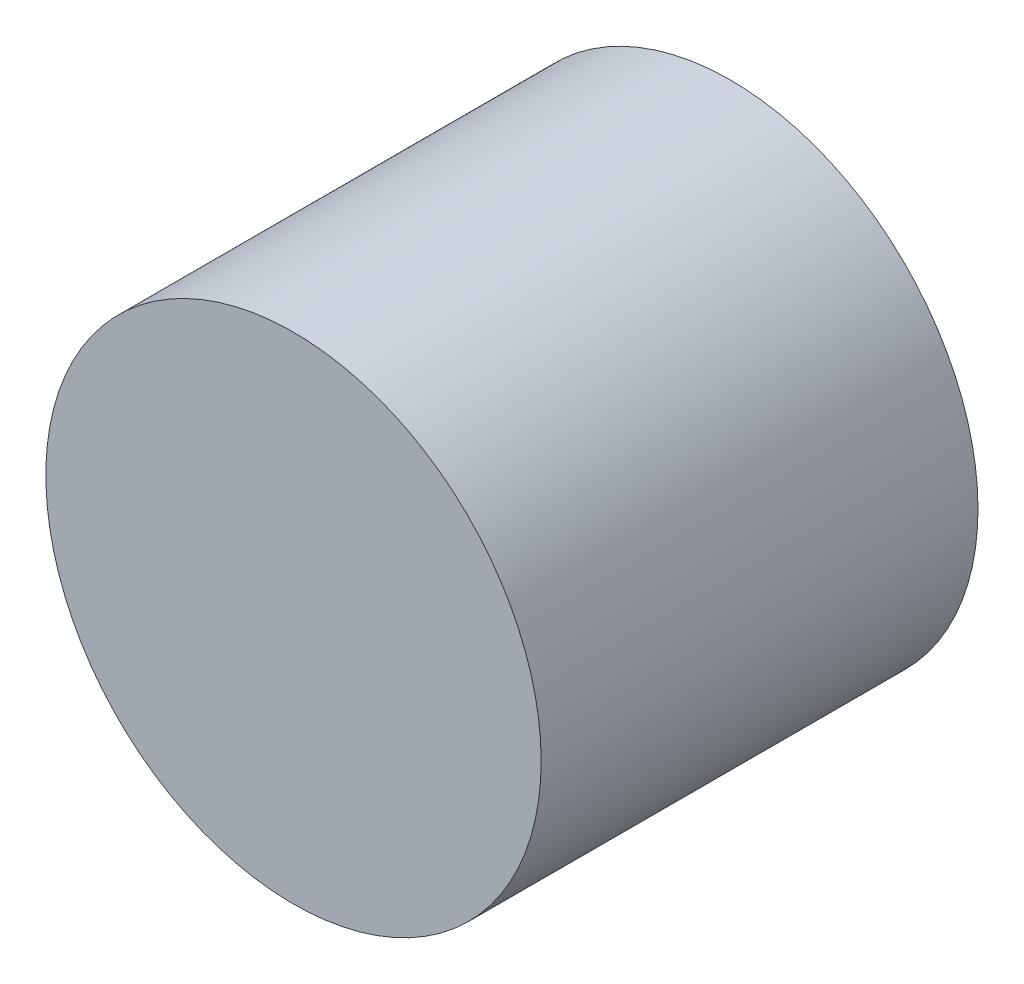
SolidWorks part; units mm, degrees
ref_plane "Front Plane" through (0, 0, 0) normal (0, 0, 1) x (1, 0, 0)
ref_plane "Top Plane" through (0, 0, 0) normal (0, 1, 0) x (1, 0, 0)
ref_plane "Right Plane" through (0, 0, 0) normal (1, 0, 0) x (0, 0, -1)
sketch "Sketch1" plane through (0, 0, 0) normal (0, 0, 1) x (1, 0, 0)
  circle A0 centre (0, 0) radius 7.2
  dimension "D1" = 14.4
extrude "Boss-Extrude1" add sketch "Sketch1" along normal blind 12.7
